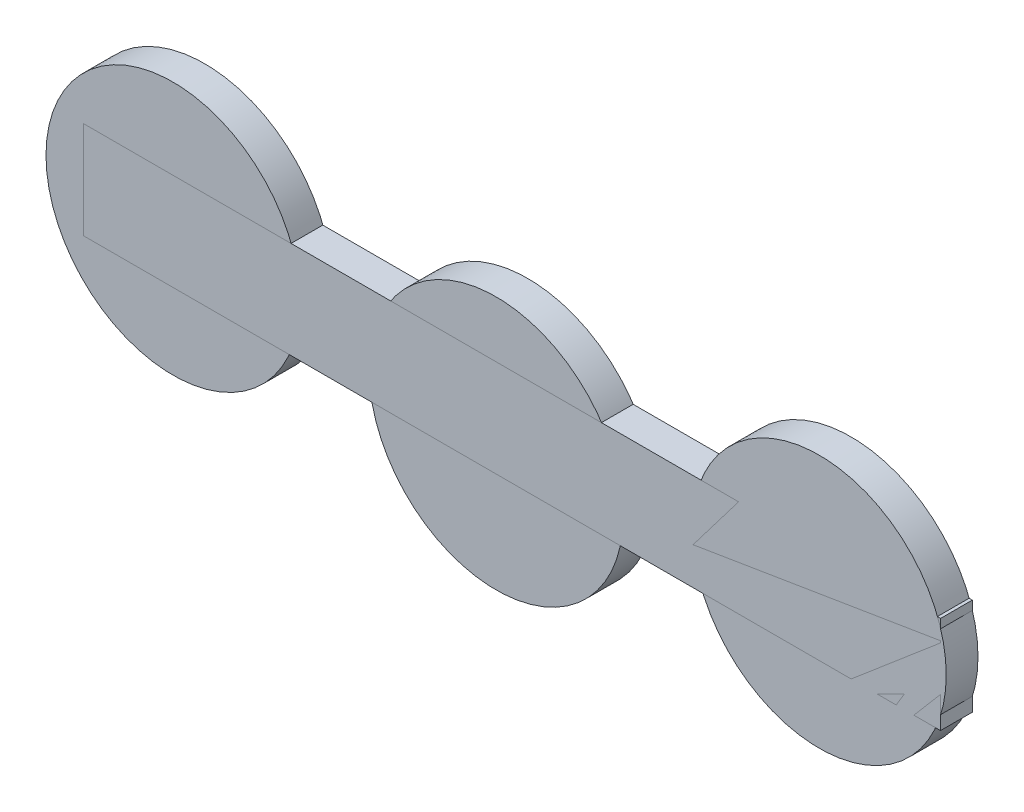
SolidWorks part; units mm, degrees
ref_plane "Front Plane" through (0, 0, 0) normal (0, 0, 1) x (1, 0, 0)
ref_plane "Top Plane" through (0, 0, 0) normal (0, 1, 0) x (1, 0, 0)
ref_plane "Right Plane" through (0, 0, 0) normal (1, 0, 0) x (0, 0, -1)
sketch "Sketch2" plane through (0, 0, 0) normal (0, 0, 1) x (1, 0, 0)
  line L0 (-356.362, -59.944) -> (-356.362, 55.703) construction
  line L1 (-0.762, -81.153) -> (-686.562, -81.153)
  line L2 (-0.762, -81.153) -> (-0.762, -3.429)
  line L3 (-0.762, -3.429) -> (-686.562, -3.429)
  line L4 (-686.562, -81.153) -> (-686.562, -3.429)
  line L5 (-356.362, -59.944) -> (-0.762, -59.944) construction
  circle A3 centre (-614.9328, -40.386) radius 14.2875
  circle A4 centre (-356.362, -59.944) radius 14.2875
  circle A5 centre (-97.7912, -40.386) radius 14.2875
  dimension "D6" = 19.558
  dimension "D1" = 77.724
  dimension "D2" = 685.8
  dimension "D3" = 258.5708
  dimension "D4" = 258.5708
  dimension "D5" = 355.6
  dimension "D7" = 19.558
  dimension "D8" = 21.209
sketch "Sketch3" plane through (0, 0, 0) normal (0, 0, 1) x (1, 0, 0)
  circle A0 centre (-97.7912, -40.386) radius 101.6
  circle A1 centre (-356.362, -59.944) radius 101.6
  circle A2 centre (-614.9328, -40.386) radius 101.6
  dimension "D1" = 203.2
sketch "Sketch4" plane through (0, 0, 0) normal (0, 0, 1) x (1, 0, 0)
  circle A0 centre (-97.7912, -40.386) radius 101.6 construction
  circle A1 centre (-356.362, -59.944) radius 101.6 construction
  circle A2 centre (-614.9328, -40.386) radius 101.6 construction
  circle A3 centre (-97.7912, -40.386) radius 101.6
  circle A4 centre (-356.362, -59.944) radius 101.6
  circle A5 centre (-614.9328, -40.386) radius 101.6
extrude "Boss-Extrude1" add sketch "Sketch4" along normal blind 25.4
sketch "Sketch5" plane through (0, 0, 0) normal (0, 0, 1) x (1, 0, 0)
  line L0 (-0.762, -3.429) -> (-686.562, -3.429) construction
  line L1 (-0.762, -81.153) -> (-686.562, -81.153) construction
  line L2 (-0.762, -81.153) -> (-0.762, -3.429) construction
  line L3 (-686.562, -81.153) -> (-686.562, -3.429) construction
  line L4 (-0.762, -3.429) -> (-686.562, -3.429)
  line L5 (-0.762, -81.153) -> (-686.562, -81.153)
  line L6 (-0.762, -81.153) -> (-0.762, -3.429)
  line L7 (-686.562, -81.153) -> (-686.562, -3.429)
extrude "Boss-Extrude2" add sketch "Sketch5" along normal blind 25.4 separate body
